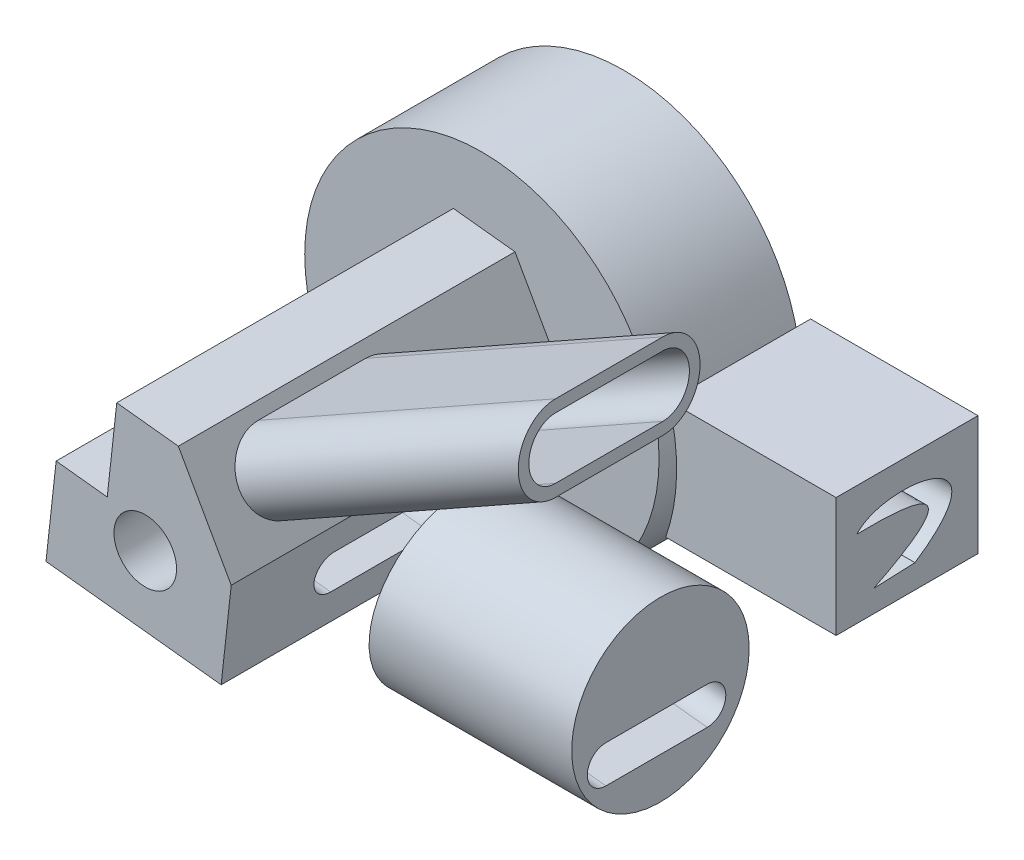
SolidWorks part; units mm, degrees
ref_plane "Front Plane" through (0, 0, 0) normal (0, 0, 1) x (1, 0, 0)
ref_plane "Top Plane" through (0, 0, 0) normal (0, 1, 0) x (1, 0, 0)
ref_plane "Right Plane" through (0, 0, 0) normal (1, 0, 0) x (0, 0, -1)
sketch "Sketch1" plane through (0, 0, 0) normal (0, 0, 1) x (1, 0, 0)
  circle A0 centre (0, 0) radius 50
extrude "Boss-Extrude2" add sketch "Sketch1" along normal blind 40
ref_plane "Plane1" through (100, 0, 0) normal (1, 0, 0) x (0, 0, -1)
sketch "Sketch2" plane through (100, 0, 0) normal (1, 0, 0) x (0, 0, -1)
  line L0 (0, -50) -> (0, 50) construction
  line L1 (-40.045, 15.5489) -> (0, 15.5489)
  line L2 (-40.045, 15.5489) -> (-40.045, -18.1716)
  line L3 (-40.045, -18.1716) -> (0, -18.1716)
  line L4 (0, 15.5489) -> (0, -18.1716)
  line L5 (-40.045, 15.5489) -> (0, -18.1716) construction
  line L6 (-40.045, -18.1716) -> (0, 15.5489) construction
  point P0 (-20.0225, -1.3114)
extrude "Boss-Extrude3" add sketch "Sketch2" against normal offset from surface (47.2437 mm away) 5 separate body
sketch "Sketch3" plane through (0, 0, 40) normal (0, 0, 1) x (1, 0, 0)
  line L0 (-10.7286, 7.7911) -> (-8.0444, 32.168)
  line L1 (-8.0444, 32.168) -> (9.3342, 30.2544)
  line L2 (9.3342, 30.2544) -> (24.2566, 3.7327)
  line L3 (24.2566, 3.7327) -> (21.4193, -22.0332)
  line L4 (21.4193, -22.0332) -> (-28.0106, -16.5902)
  line L5 (-28.0106, -16.5902) -> (-25.1509, 9.3792)
  line L6 (-25.1509, 9.3792) -> (-10.7286, 7.7911)
  line L8 (33.508, -22.9364) -> (36.6175, 17.5506)
  line L9 (36.6175, 17.5506) -> (3.1095, 40.4869)
  line L10 (3.1095, 40.4869) -> (-33.508, 22.9364)
  line L11 (-33.508, 22.9364) -> (-36.6175, -17.5506)
  line L12 (-36.6175, -17.5506) -> (-3.1095, -40.4869)
  line L13 (-3.1095, -40.4869) -> (33.508, -22.9364)
  circle A0 centre (0, 0) radius 35.166 construction
  point P8 (12.548, -4.8683)
  point P17 (28.7703, 3.0898)
  point P18 (25.8625, -19.4836)
  point P19 (11.1707, 26.4284)
extrude "Boss-Extrude7" add sketch "Sketch3" along normal blind 95 contours L11 L12 L3 L2 L9 L10 L0 L6
sketch "Sketch5" plane through (0, 0, 135) normal (0, 0, 1) x (1, 0, 0)
  circle A0 centre (0, 0) radius 8.835
extrude "Cut-Extrude1" cut sketch "Sketch5" against normal through all draft 3 draft outward yes
sketch "Sketch6" plane through (100, 0, 0) normal (1, 0, 0) x (0, 0, -1)
  line L0 (-29.4384, -11.9638) -> (-17.7947, -11.4876)
  spline S0 degree 3 poles (-34.1746, 3.6533) (-26.4698, 12.6113) (10.2482, 7.1847) (-17.7947, -11.4876) knots 0 0 0 0 1 1 1 1
  spline S1 degree 2 poles (-29.4384, -11.9638) (3.6575, 4.5376) (-34.1746, 3.6533) knots 0 0 0 1 1 1
  point P6 (-23.5579, -10.2442)
  point P7 (-13.0196, -10.2442)
  point P8 (-14.0276, 0)
  point P9 (0, 0)
  point P10 (0, 0)
extrude "Cut-Extrude2" cut sketch "Sketch6" against normal up to surface (92.0449 mm away)
sketch "Sketch7" plane through (20.0192, 11.2638, 0) normal (0.8715, 0.4904, 0) x (0, 0, -1)
  line L0 (-114.2425, 7.6499) -> (-83.9464, 7.6499) construction
  line L1 (-114.2425, 15.1517) -> (-83.9464, 15.1517)
  line L2 (-114.2425, 0.148) -> (-83.9464, 0.148)
  arc A0 (-114.2425, 15.1517) -> (-114.2425, 0.148) centre (-114.2425, 7.6499) ccw
  arc A1 (-83.9464, 0.148) -> (-83.9464, 15.1517) centre (-83.9464, 7.6499) ccw
  point P2 (-99.0945, 7.6499)
extrude "Extrude-Thin2" add sketch "Sketch7" along normal offset from surface (96.2475 mm away) 5 thin up to plane "Plane1" thin type one direction wall 3
sketch "Sketch8" plane through (20.0192, 11.2638, 0) normal (0.8715, 0.4904, 0) x (0, 0, -1)
  ellipse E0 centre (-100.9355, 7.9174) end of major axis (-95.6439, 7.9174) minor radius 2.7661
extrude "Cut-Extrude3" cut sketch "Sketch8" against normal through all draft 7
sketch "Sketch9" plane through (100, 0, 0) normal (1, 0, 0) x (0, 0, -1)
  circle A0 centre (-89.6179, -9.047) radius 25.0431
extrude "Boss-Extrude9" add sketch "Sketch9" against normal offset from surface (57.0298 mm away) 20 separate body
sketch "Sketch10" plane through (43.4397, -4.7834, 0) normal (-0.994, 0.1095, 0) x (0, 0, 1)
  line L0 (76.4186, -6.1087) -> (105.0106, -6.1087) construction
  line L1 (76.4186, -0.8625) -> (105.0106, -0.8625)
  line L2 (76.4186, -11.355) -> (105.0106, -11.355)
  arc A0 (76.4186, -0.8625) -> (76.4186, -11.355) centre (76.4186, -6.1087) ccw
  arc A1 (105.0106, -11.355) -> (105.0106, -0.8625) centre (105.0106, -6.1087) ccw
  point P2 (90.7146, -6.1087)
extrude "Cut-Extrude5" cut sketch "Sketch10" along normal blind 49 and the other way blind 71
